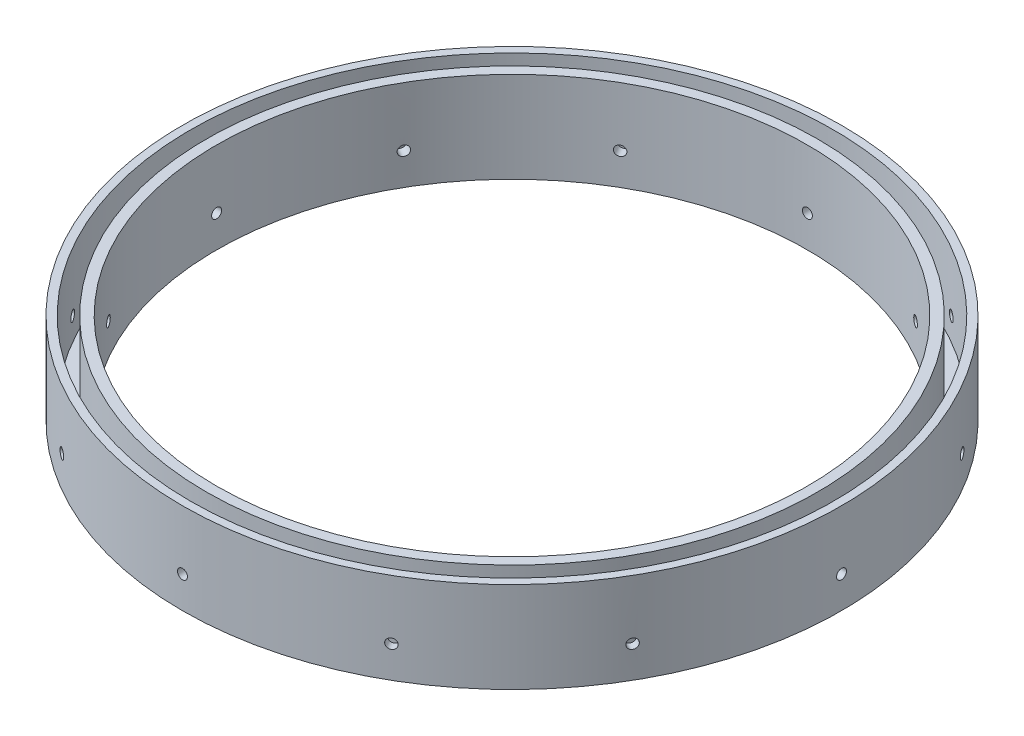
SolidWorks part; units mm, degrees
ref_plane "Front Plane" through (0, 0, 0) normal (0, 0, 1) x (1, 0, 0)
ref_plane "Top Plane" through (0, 0, 0) normal (0, 1, 0) x (1, 0, 0)
ref_plane "Right Plane" through (0, 0, 0) normal (1, 0, 0) x (0, 0, -1)
sketch "Sketch1" plane through (0, 0, 0) normal (0, 1, 0) x (1, 0, 0)
  circle A0 centre (0, 0) radius 92.075
  circle A1 centre (0, 0) radius 82.55
  dimension "D1" = 184.15
  dimension "D2" = 165.1
extrude "Boss-Extrude1" add sketch "Sketch1" along normal blind 25.4
sketch "Sketch2" plane through (0, 25.4, 0) normal (0, 1, 0) x (1, 0, 0)
  circle A0 centre (0, 0) radius 85.4075
  circle A1 centre (0, 0) radius 89.8525
  dimension "D1" = 179.705
  dimension "D2" = 170.815
extrude "Cut-Extrude1" cut sketch "Sketch2" against normal blind 22.86
sketch "Sketch3" plane through (0, 0, 0) normal (0, 0, 1) x (1, 0, 0)
  line L0 (92.075, 25.4) -> (-92.075, 25.4) construction
  circle A0 centre (0, 8.89) radius 1.3843
  dimension "D1" = 2.7686
  dimension "D2" = 16.51
extrude "Cut-Extrude2" cut sketch "Sketch3" against normal up to surface (92.0646 mm away)
pattern_circular "CirPattern1" count 12 over 360 about axis through (0, 25.4, 0) along (0, 1, 0) of "Cut-Extrude2"
